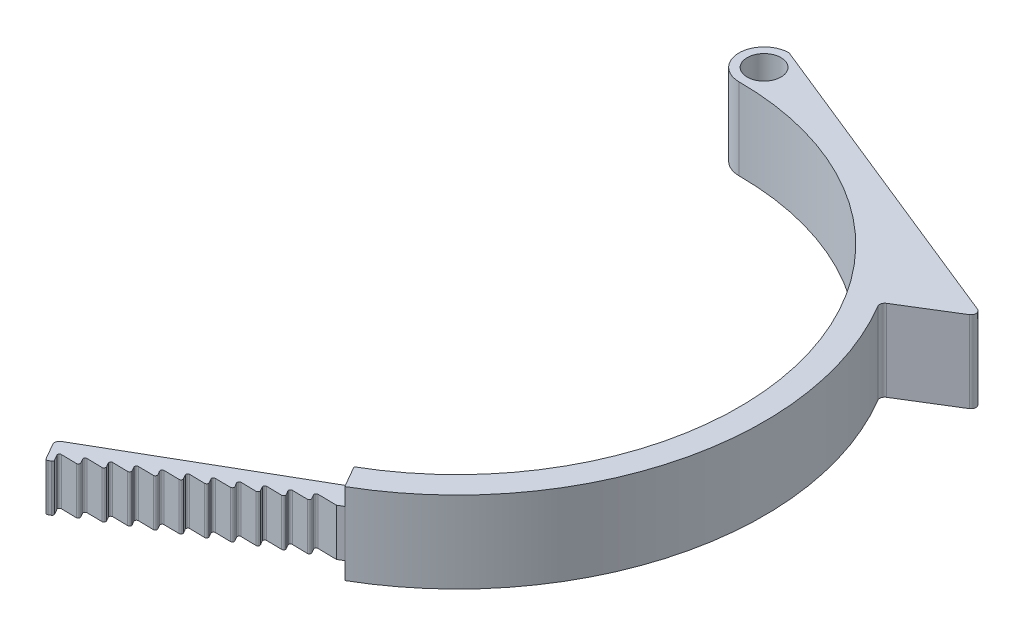
SolidWorks part; units mm, degrees
ref_plane "Front Plane" through (0, 0, 0) normal (0, 0, 1) x (1, 0, 0)
ref_plane "Top Plane" through (0, 0, 0) normal (0, 1, 0) x (1, 0, 0)
ref_plane "Right Plane" through (0, 0, 0) normal (1, 0, 0) x (0, 0, -1)
sketch "Sketch1" plane through (0, 0, 0) normal (0, 1, 0) x (1, 0, 0)
  line L0 (0, 0) -> (22.5, -38.9711) construction
  line L1 (0, 0) -> (0, -45) construction
  line L2 (0, 0) -> (41.4964, -71.8739) construction
  line L3 (0, 53) -> (51.921, 32.0189)
  line L4 (51.921, 32.0189) -> (41.707, 25.7201)
  line L5 (0, 53) -> (0, 49)
  line L7 (0, 49) -> (0, 53)
  line L8 (22.5, -38.9711) -> (-7.8109, -56.4711)
  line L9 (-7.8109, -56.4711) -> (-5.8109, -59.9352)
  line L10 (-5.8109, -59.9352) -> (24.5, -42.4352)
  circle A0 centre (0, 0) radius 45 construction
  arc A1 (0, 45) -> (22.5, -38.9711) centre (0, 0) cw
  arc A2 (0, 45) -> (0, 53) centre (0, 49) cw
  arc A4 (24.5, -42.4352) -> (0, 49) centre (0, 0) ccw
  circle A5 centre (0, 49) radius 2.7
  arc A6 (41.707, 25.7201) -> (0, 49) centre (0, 0) ccw
  point P9 (-6.8109, -58.2032)
  dimension "D1" = 90
  dimension "D5" = 56
  dimension "D6" = 5.4
  dimension "D2" = 30
  dimension "D3" = 8
  dimension "D4" = 4
  dimension "D7" = 12
  dimension "D8" = 35
extrude "Boss-Extrude1" add sketch "Sketch1" along normal blind 13
sketch "Sketch2" plane through (0, 13, 0) normal (0, 1, 0) x (1, 0, 0)
  line L0 (-4.9449, -59.4352) -> (-5.8449, -57.8764)
  line L1 (-5.8109, -59.9352) -> (24.5, -42.4352) construction
  line L2 (-5.8449, -57.8764) -> (-2.3468, -57.9352)
  line L3 (-2.3468, -57.9352) -> (-4.9449, -59.4352)
  line L4 (-7.8109, -56.4711) -> (-5.8109, -59.9352) construction
  line L29 (0.2513, -56.4352) -> (-2.3468, -57.9352)
  line L30 (-2.3468, -57.9352) -> (-3.2468, -56.3764)
  line L31 (-3.2468, -56.3764) -> (0.2513, -56.4352)
  line L32 (2.8494, -54.9352) -> (0.2513, -56.4352)
  line L33 (0.2513, -56.4352) -> (-0.6487, -54.8764)
  line L34 (-0.6487, -54.8764) -> (2.8494, -54.9352)
  line L35 (5.4474, -53.4352) -> (2.8494, -54.9352)
  line L36 (2.8494, -54.9352) -> (1.9494, -53.3764)
  line L37 (1.9494, -53.3764) -> (5.4474, -53.4352)
  line L38 (8.0455, -51.9352) -> (5.4474, -53.4352)
  line L39 (5.4474, -53.4352) -> (4.5474, -51.8764)
  line L40 (4.5474, -51.8764) -> (8.0455, -51.9352)
  line L41 (10.6436, -50.4352) -> (8.0455, -51.9352)
  line L42 (8.0455, -51.9352) -> (7.1455, -50.3764)
  line L43 (7.1455, -50.3764) -> (10.6436, -50.4352)
  line L44 (13.2417, -48.9352) -> (10.6436, -50.4352)
  line L45 (10.6436, -50.4352) -> (9.7436, -48.8764)
  line L46 (9.7436, -48.8764) -> (13.2417, -48.9352)
  line L47 (15.8397, -47.4352) -> (13.2417, -48.9352)
  line L48 (13.2417, -48.9352) -> (12.3417, -47.3764)
  line L49 (12.3417, -47.3764) -> (15.8397, -47.4352)
  line L50 (18.4378, -45.9352) -> (15.8397, -47.4352)
  line L51 (15.8397, -47.4352) -> (14.9397, -45.8764)
  line L52 (14.9397, -45.8764) -> (18.4378, -45.9352)
  line L53 (21.0359, -44.4352) -> (18.4378, -45.9352)
  line L54 (18.4378, -45.9352) -> (17.5378, -44.3764)
  line L55 (17.5378, -44.3764) -> (21.0359, -44.4352)
  line L56 (23.634, -42.9352) -> (21.0359, -44.4352)
  line L57 (21.0359, -44.4352) -> (20.1359, -42.8764)
  line L58 (20.1359, -42.8764) -> (23.634, -42.9352)
  line L59 (-2.3468, -57.9352) -> (0.2513, -56.4352) construction
  line M10 (-5.8109, -59.9352) -> (24.5, -42.4352)
  dimension "D1" = 1.8
  dimension "D2" = 3
  dimension "D3" = 1
  dimension "D5" = 3
  dimension "D4" = 11
extrude "Cut-Extrude3" cut sketch "Sketch2" against normal through all contours L2 L0 M10 | L31 L30 M10 | L34 L33 M10 | L37 L36 M10 | L40 L39 M10 | L43 L42 M10 | L46 L45 M10 | L49 L48 M10 | L52 L51 M10 | L55 L54 M10 | L58 L57 M10
fillet "Fillet2" radius 0.3 23 edges at (20.1359, 6.5, 42.8764) (21.0359, 6.5, 44.4352) (17.5378, 6.5, 44.3764) (18.4378, 6.5, 45.9352) (14.9397, 6.5, 45.8764) (15.8397, 6.5, 47.4352) (12.3417, 6.5, 47.3764) (13.2417, 6.5, 48.9352) (9.7436, 6.5, 48.8764) (10.6436, 6.5, 50.4352) (7.1455, 6.5, 50.3764) (8.0455, 6.5, 51.9352) (4.5474, 6.5, 51.8764) (5.4474, 6.5, 53.4352) (1.9494, 6.5, 53.3764) (2.8494, 6.5, 54.9352) (-0.6487, 6.5, 54.8764) (0.2513, 6.5, 56.4352) (-3.2468, 6.5, 56.3764) (-2.3468, 6.5, 57.9352) (-5.8449, 6.5, 57.8764) (-4.9449, 6.5, 59.4352) (-5.8109, 6.5, 59.9352)
fillet "Fillet1" radius 0.8 4 edges at (0, 6.5, -53) (51.921, 6.5, -32.0189) (41.707, 6.5, -25.7201) (-7.8109, 6.5, 56.4711)
sketch "Sketch3" plane through (-30.3109, 0, 17.5) normal (-0.866, 0, 0.5) x (0.5, 0, 0.866)
  line L0 (45.8, 13) -> (48.7, 13) construction
  line L1 (44.1864, 10.25) -> (50.0968, 10.25)
  line L2 (44.1864, 10.25) -> (44.1864, 2.75)
  line L3 (44.1864, 2.75) -> (50.0968, 2.75)
  line L4 (50.0968, 10.25) -> (50.0968, 2.75)
  dimension "D1" = 7.5
  dimension "D2" = 2.75
extrude "Cut-Extrude2" cut sketch "Sketch3" against normal blind 35 flip side to cut
